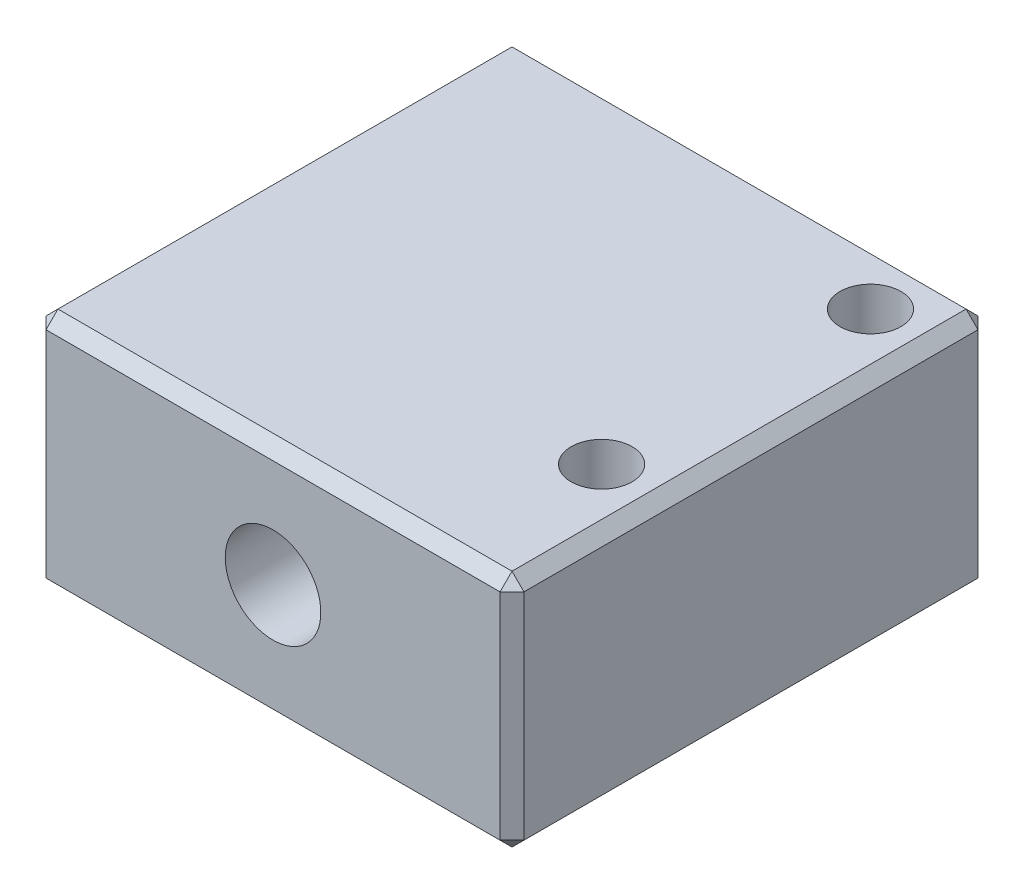
SolidWorks part; units mm, degrees
ref_plane "Front Plane" through (0, 0, 0) normal (0, 0, 1) x (1, 0, 0)
ref_plane "Top Plane" through (0, 0, 0) normal (0, 1, 0) x (1, 0, 0)
ref_plane "Right Plane" through (0, 0, 0) normal (1, 0, 0) x (0, 0, -1)
sketch "Sketch1" plane through (0, 0, 0) normal (0, 1, 0) x (1, 0, 0)
  line L1 (-20, -20) -> (20, -20)
  line L2 (-20, -20) -> (-20, 20)
  line L3 (-20, 20) -> (20, 20)
  line L4 (20, -20) -> (20, 20)
  line L5 (-20, -20) -> (20, 20) construction
  line L6 (-20, 20) -> (20, -20) construction
  point P0 (0, 0)
  dimension "D1" = 40
  dimension "D2" = 40
extrude "Boss-Extrude1" add sketch "Sketch1" along normal blind 20
sketch "Sketch2" plane through (-20, 0, 0) normal (-1, 0, 0) x (0, 0, 1)
  line L0 (-20, 0) -> (20, 0) construction
  line L1 (-20, 20) -> (-20, 0) construction
  circle A0 centre (-10, 10) radius 5.6
  dimension "D1" = 11.2
  dimension "D2" = 10
  dimension "D3" = 10
extrude "Cut-Extrude1" cut sketch "Sketch2" against normal blind 10
chamfer "Chamfer1" distance 1 angle 45 12 edges at (20, 10, -20) (20, 0, 0) (20, 10, 20) (20, 20, 0) (0, 0, 20) (0, 0, -20) (0, 20, -20) (0, 20, 20) (-20, 10, 20) (-20, 0, 0) (-20, 10, -20) (-20, 20, 0)
hole_wizard "1/4-20 Tapped Hole1" positions "Sketch4" profile "Sketch3" tap size "1/4-20" standard "ANSI Inch" end condition through all
sketch "Sketch4" plane through (0, 20, 0) normal (0, 1, 0) x (1, 0, 0)
  line L0 (19, -20) -> (-19, -20) construction
  line L1 (20, 19) -> (20, -19) construction
  line L2 (-19, 20) -> (19, 20) construction
  point P0 (15, -7.5)
  point P7 (15, 15)
  dimension "D1" = 12.5
  dimension "D2" = 5
  dimension "D3" = 5
sketch "Sketch3" plane through (15, 20, 7.5) normal (1, 0, 0) x (0, 0, 1)
  line L0 (0, 0) -> (0, 20)
  line L1 (0, 20) -> (2.5527, 20)
  line L2 (2.5527, 20) -> (2.5527, 0)
  line L5 (2.5527, 0) -> (0, 0)
  line L11 (0, -6.35) -> (0, 107.95) construction
  dimension "Thru Tap Drill Dia." = 5.1054
  dimension "Thru Tap Drill Depth" = 20
cosmetic thread "Hole Thread1" parameters "D2"=6.35
cosmetic thread "Hole Thread2" parameters "D2"=6.35
sketch "Sketch5" plane through (0, 0, -20) normal (0, 0, -1) x (-1, 0, 0)
  line L1 (-20, 1) -> (-20, 19) construction
  line L2 (19, 0) -> (-19, 0) construction
  circle A0 centre (0, 10) radius 4
  dimension "D1" = 8
  dimension "D2" = 10
  dimension "D3" = 20
extrude "Cut-Extrude2" cut sketch "Sketch5" against normal through all
